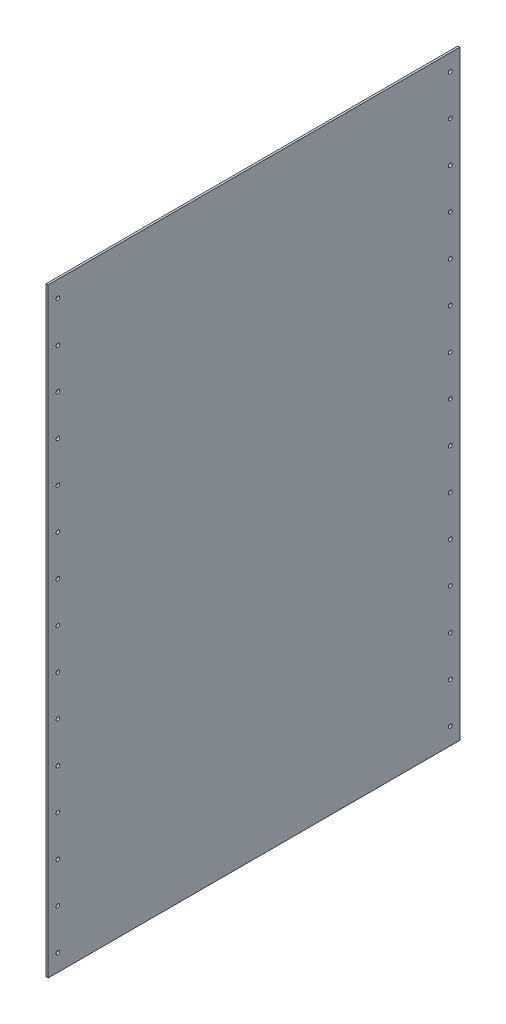
SolidWorks part; units mm, degrees
ref_plane "Front" through (0, 0, 0) normal (0, 0, 1) x (1, 0, 0)
ref_plane "Top" through (0, 0, 0) normal (0, 1, 0) x (1, 0, 0)
ref_plane "Right" through (0, 0, 0) normal (1, 0, 0) x (0, 0, -1)
sketch "Sketch1" plane through (0, 0, 0) normal (1, 0, 0) x (0, 0, -1)
  line L1 (0, 0) -> (609.6, 0)
  line L2 (0, 0) -> (0, 889)
  line L3 (0, 889) -> (609.6, 889)
  line L4 (609.6, 0) -> (609.6, 889)
  dimension "D1" = 889
  dimension "D2" = 609.6
extrude "Boss-Extrude1" add sketch "Sketch1" along normal blind 3
sketch "Sketch2" plane through (3, 0, 0) normal (1, 0, 0) x (0, 0, -1)
  line L0 (304.8, 0) -> (304.8, 25.4) construction
  line L1 (0, 0) -> (609.6, 0) construction
  line L2 (14.2875, 25.4) -> (595.3125, 25.4) construction
  line L3 (595.3125, 25.4) -> (609.6, 25.4) construction
  line L4 (609.6, 0) -> (609.6, 889) construction
  line L5 (14.2875, 25.4) -> (0, 25.4) construction
  line L6 (0, 889) -> (0, 0) construction
  line L7 (14.2875, 25.4) -> (595.3125, 25.4) construction
  circle A0 centre (14.2875, 25.4) radius 2.667
  circle A1 centre (595.3125, 25.4) radius 2.667
  circle A2 centre (595.3125, 85.344) radius 2.667
  circle A3 centre (595.3125, 145.288) radius 2.667
  circle A4 centre (595.3125, 205.232) radius 2.667
  circle A5 centre (595.3125, 265.176) radius 2.667
  circle A6 centre (595.3125, 325.12) radius 2.667
  circle A7 centre (595.3125, 385.064) radius 2.667
  circle A8 centre (595.3125, 445.008) radius 2.667
  circle A9 centre (595.3125, 504.952) radius 2.667
  circle A10 centre (595.3125, 564.896) radius 2.667
  circle A11 centre (595.3125, 624.84) radius 2.667
  circle A12 centre (595.3125, 684.784) radius 2.667
  circle A13 centre (595.3125, 744.728) radius 2.667
  circle A14 centre (595.3125, 804.672) radius 2.667
  circle A15 centre (595.3125, 864.616) radius 2.667
  circle A16 centre (14.2875, 85.344) radius 2.667
  circle A17 centre (14.2875, 145.288) radius 2.667
  circle A18 centre (14.2875, 205.232) radius 2.667
  circle A19 centre (14.2875, 265.176) radius 2.667
  circle A20 centre (14.2875, 325.12) radius 2.667
  circle A21 centre (14.2875, 385.064) radius 2.667
  circle A22 centre (14.2875, 445.008) radius 2.667
  circle A23 centre (14.2875, 504.952) radius 2.667
  circle A24 centre (14.2875, 564.896) radius 2.667
  circle A25 centre (14.2875, 624.84) radius 2.667
  circle A26 centre (14.2875, 684.784) radius 2.667
  circle A27 centre (14.2875, 744.728) radius 2.667
  circle A28 centre (14.2875, 804.672) radius 2.667
  circle A29 centre (14.2875, 864.616) radius 2.667
  dimension "D3" = 5.334
  dimension "D1" = 25.4
  dimension "=D6" = 581.025
  dimension "D6" = 581.025
  dimension "D4" = 2
  dimension "D5" = 15
extrude "Cut-Extrude1" cut sketch "Sketch2" against normal up to next (3 mm away)
